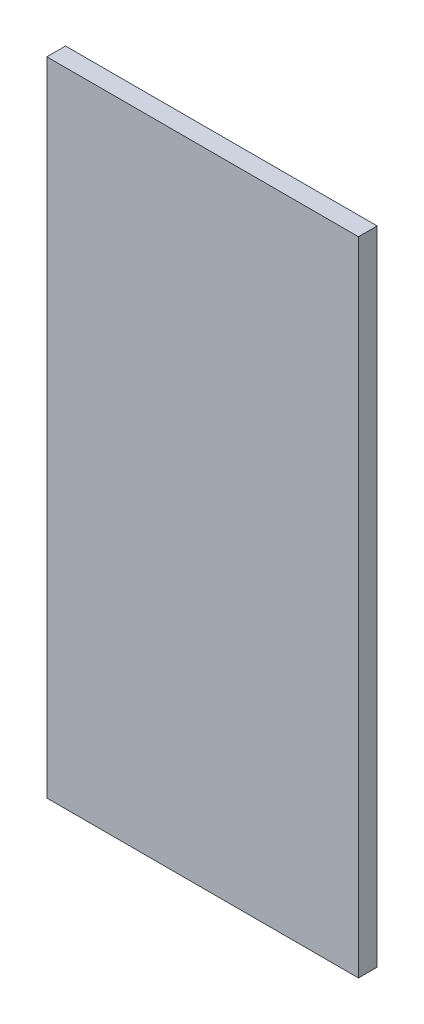
SolidWorks part; units mm, degrees
ref_plane "Front Plane" through (0, 0, 0) normal (0, 0, 1) x (1, 0, 0)
ref_plane "Top Plane" through (0, 0, 0) normal (0, 1, 0) x (1, 0, 0)
ref_plane "Right Plane" through (0, 0, 0) normal (1, 0, 0) x (0, 0, -1)
sketch "Sketch1" plane through (0, 0, 0) normal (0, 0, 1) x (1, 0, 0)
  line L1 (-10, 199.4274) -> (90, 199.4274)
  line L2 (-10, 199.4274) -> (-10, -6.5726)
  line L3 (-10, -6.5726) -> (90, -6.5726)
  line L4 (90, 199.4274) -> (90, -6.5726)
  dimension "D1" = 100
  dimension "D2" = 206
extrude "Boss-Extrude1" add sketch "Sketch1" along normal blind 6
